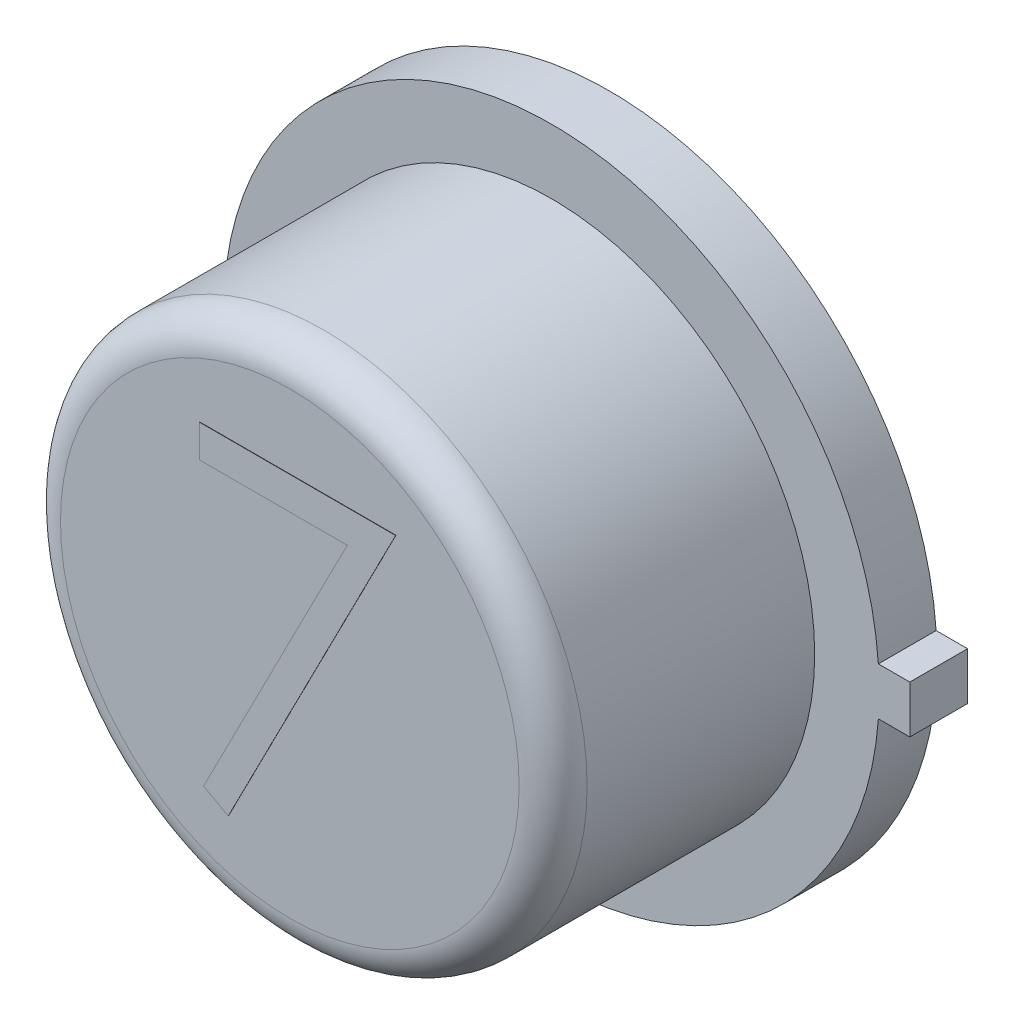
SolidWorks part; units mm, degrees
ref_plane "Front Plane" through (0, 0, 0) normal (0, 0, 1) x (1, 0, 0)
ref_plane "Top Plane" through (0, 0, 0) normal (0, 1, 0) x (1, 0, 0)
ref_plane "Right Plane" through (0, 0, 0) normal (1, 0, 0) x (0, 0, -1)
sketch "Sketch1" plane through (0, 0, 0) normal (0, 0, 1) x (1, 0, 0)
  line L1 (2.4511, 0.1778) -> (2.6797, 0.1778)
  line L3 (2.4511, -0.1778) -> (2.6797, -0.1778)
  line L4 (2.6797, 0.1778) -> (2.6797, -0.1778)
  line L5 (2.4511, 0.1778) -> (2.4444, 0.1778)
  line L6 (2.4511, -0.1778) -> (2.4446, -0.1778)
  arc A0 (2.4446, 0.1778) -> (2.4446, -0.1778) centre (0, 0) ccw
  dimension "D1" = 4.9022
  dimension "D2" = 0.3556
  dimension "D3" = 0.2286
extrude "Boss-Extrude1" add sketch "Sketch1" along normal blind 0.4318
sketch "Sketch2" plane through (0, 0, 0.4318) normal (0, 0, 1) x (1, 0, 0)
  circle A0 centre (0, 0) radius 1.9685
  dimension "D1" = 3.937
extrude "Boss-Extrude2" add sketch "Sketch2" along normal blind 1.9558
sketch "Sketch3" plane through (0, 0, 0) normal (0, 0, -1) x (-1, 0, 0)
  circle A0 centre (0, 0) radius 1.7576
extrude "Boss-Extrude3" add sketch "Sketch3" along normal blind 0.0025
fillet "Fillet1" radius 0.254 1 edges at (1.9685, 0, 2.3876)
sketch "Sketch4" plane through (0, 0, 2.3876) normal (0, 0, 1) x (1, 0, 0)
  line L0 (-1.2065, -1.2181) -> (1.2065, -1.2181) construction
  circle A0 centre (0, 0) radius 1.7145 construction
  text T0 "7" font "Century Gothic" height in points 9
  dimension "D1" = 2.413
extrude "Boss-Extrude6" add sketch "Sketch4" along normal blind 0.0025
